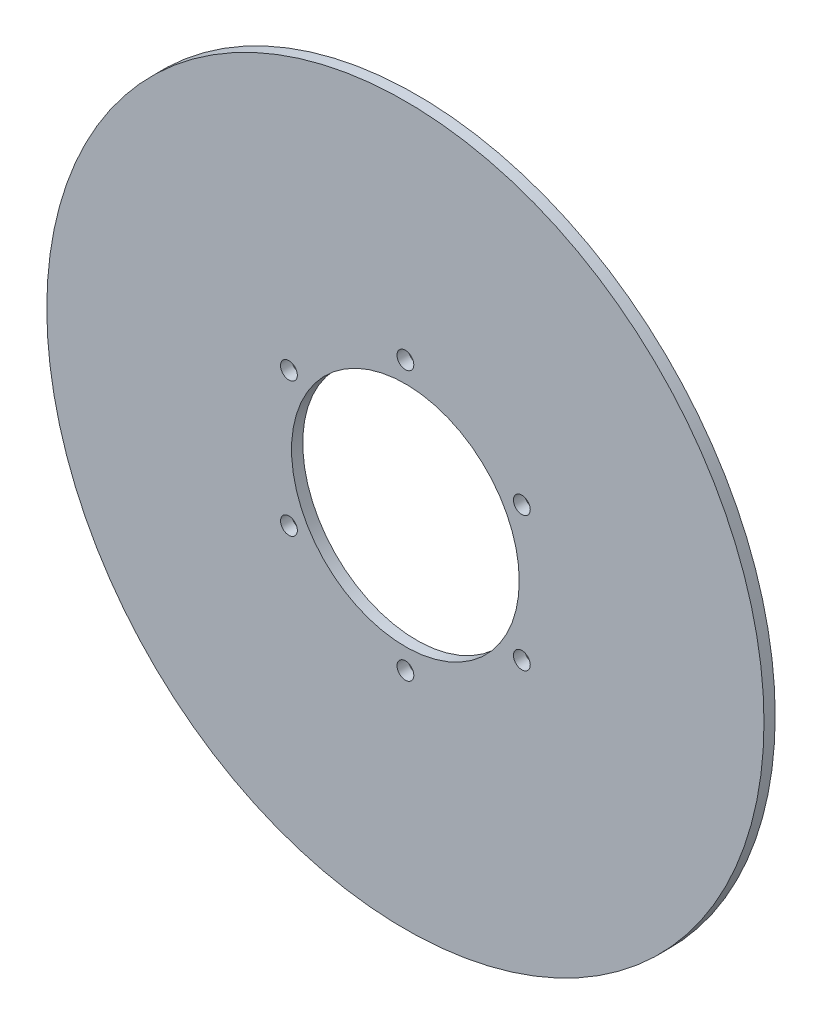
SolidWorks part; units mm, degrees
ref_plane "Front Plane" through (0, 0, 0) normal (0, 0, 1) x (1, 0, 0)
ref_plane "Top Plane" through (0, 0, 0) normal (0, 1, 0) x (1, 0, 0)
ref_plane "Right Plane" through (0, 0, 0) normal (1, 0, 0) x (0, 0, -1)
sketch "Sketch1" plane through (0, 0, 0) normal (0, 0, 1) x (1, 0, 0)
  circle A0 centre (0, 0) radius 16.129
  circle A1 centre (0, 0) radius 50.8
  dimension "D1" = 32.258
  dimension "D2" = 101.6
extrude "Boss-Extrude1" add sketch "Sketch1" along normal blind 1.5875
hole_wizard "3/32 (0.09375) Diameter Hole1" positions "Sketch3" profile "Sketch2" hole size "3/32" standard "Ansi Inch"
sketch "Sketch3" plane through (0, 0, 1.5875) normal (0, 0, 1) x (1, 0, 0)
  point P1 (0, 19.05)
  dimension "D1" = 19.05
sketch "Sketch2" plane through (0, 19.05, 1.5875) normal (1, 0, 0) x (0, -1, 0)
  line L0 (0, 0) -> (0, 26.1154)
  line L1 (0, 26.1154) -> (1.1906, 25.4)
  line L2 (1.1906, 25.4) -> (1.1906, 0)
  line L5 (1.1906, 0) -> (0, 0)
  line L10 (0, 26.1154) -> (-1.1906, 25.4) construction
  line L11 (0, -6.35) -> (0, 107.95) construction
  dimension "Hole Dia." = 2.3812
  dimension "Hole Depth" = 25.4
  dimension "Drill Angle" = 118
hole_wizard "#2 Clearance Hole1" positions "Sketch7" profile "Sketch6" hole size "#2" standard "Ansi Inch"
sketch "Sketch7" plane through (0, 0, 1.5875) normal (0, 0, 1) x (1, 0, 0)
  point P0 (0, -19.05)
  dimension "D1" = 19.05
sketch "Sketch6" plane through (0, -19.05, 1.5875) normal (1, 0, 0) x (0, -1, 0)
  line L0 (0, 0) -> (0, 26.0792)
  line L1 (0, 26.0792) -> (1.1303, 25.4)
  line L2 (1.1303, 25.4) -> (1.1303, 0)
  line L5 (1.1303, 0) -> (0, 0)
  line L10 (0, 26.0792) -> (-1.1303, 25.4) construction
  line L11 (0, -6.35) -> (0, 107.95) construction
  dimension "Hole Dia." = 2.2606
  dimension "Hole Depth" = 25.4
  dimension "Drill Angle" = 118
pattern_circular "CirPattern1" count 6 every 60 about axis through (0, 0, 0) along (0, 0, 1) of "3/32 (0.09375) Diameter Hole1"
